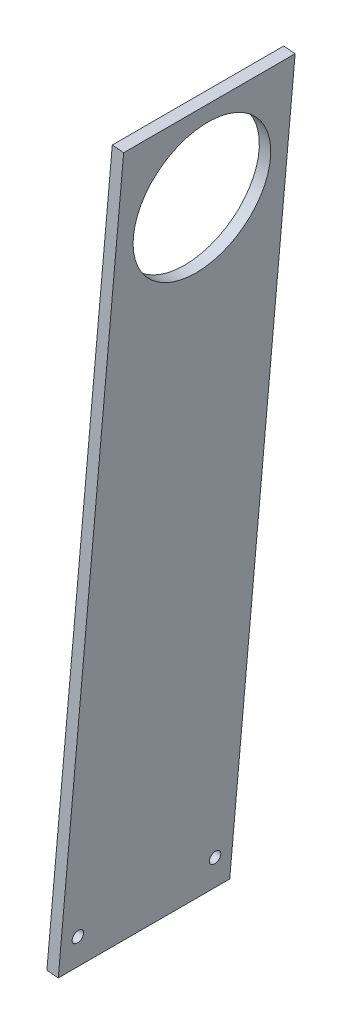
SolidWorks part; units mm, degrees
ref_plane "Front Plane" through (0, 0, 0) normal (0, 0, 1) x (1, 0, 0)
ref_plane "Top Plane" through (0, 0, 0) normal (0, 1, 0) x (1, 0, 0)
ref_plane "Right Plane" through (0, 0, 0) normal (1, 0, 0) x (0, 0, -1)
sketch "Sketch1" plane through (0, 0, 0) normal (0, 0, 1) x (1, 0, 0)
  line L0 (0, 0) -> (36.6665, 419.1) construction
  line L1 (36.6665, 419.1) -> (155.7226, 419.1) construction
  line L2 (155.7226, 419.1) -> (155.7226, 0) construction
  line L3 (155.7226, 0) -> (0, 0) construction
  line L4 (155.7226, -1000) -> (155.7226, 49000) construction
  line L5 (1.8042, 20.6221) -> (36.6665, 419.1) construction
  line L6 (1.8042, 20.6221) -> (41.652, 17.1359) construction
  line L7 (36.6665, 419.1) -> (76.5143, 415.6138) construction
  line L8 (41.652, 17.1359) -> (76.5143, 415.6138) construction
  line L9 (60.4726, -1000) -> (60.4726, 49000) construction
  line L10 (-52.7184, 317.5) -> (-128.6284, 324.1413) construction
  line L11 (-30.1965, 414.3375) -> (36.6601, 414.3375) construction
  line L12 (-1162.1335, 304.8) -> (48837.8665, 304.8) construction
  line L13 (-130.0274, 292.1) -> (-53.8274, 292.1) construction
  line L14 (-128.6284, 324.1413) -> (-53.8274, 292.1) construction
  line L15 (-52.7184, 317.5) -> (-130.0274, 292.1) construction
  line L16 (36.6601, 338.1375) -> (-30.1965, 338.1375) construction
  line L17 (-138.1172, 324.9714) -> (27.1662, 310.511)
  line L18 (-138.1172, 324.9714) -> (-137.5638, 331.2973)
  line L19 (-137.5638, 331.2973) -> (36.6665, 419.1)
  line L20 (36.6665, 419.1) -> (104.9226, 419.1)
  line L21 (104.9226, 419.1) -> (104.9226, 0) construction
  line L22 (27.1662, 310.511) -> (0.3389, 3.8741)
  line L23 (0.3389, 3.8741) -> (44.6198, 0)
  line L24 (44.6198, 0) -> (104.9226, 0)
  line L25 (104.9226, 419.1) -> (155.7226, 311.15)
  line L26 (155.7226, 311.15) -> (155.7226, 304.8)
  line L27 (155.7226, 304.8) -> (104.9226, 280.8941)
  line L28 (104.9226, 280.8941) -> (104.9226, 0)
  arc A0 (-128.6284, 324.1413) -> (-30.1965, 414.3375) centre (-30.1965, 315.5296) cw construction
  arc A1 (69.9976, 304.8) -> (36.6601, 338.1375) centre (36.6601, 304.8) ccw construction
  arc A2 (146.1976, 304.8) -> (36.6601, 414.3375) centre (36.6601, 304.8) ccw construction
  arc A3 (-52.7184, 317.5) -> (-30.1965, 338.1375) centre (-30.1965, 315.5296) cw construction
  point P7 (54.1226, 400.05)
  point P17 (146.1976, 304.8)
  point P18 (69.9976, 304.8)
  dimension "D9" = 9.525
  dimension "D14" = 25.4
  dimension "D1" = 419.1
  dimension "D2" = 101.6
  dimension "D3" = 19.05
  dimension "D4" = 19.05
  dimension "D5" = 85
  dimension "D6" = 40
  dimension "D7" = 400
  dimension "D8" = 95.25
  dimension "D10" = 9.525
  dimension "D11" = 114.3
  dimension "D12" = 76.2
  dimension "D13" = 9.525
  dimension "D15" = 127
  dimension "D16" = 9.525
  dimension "D17" = 209.55
  dimension "D18" = 6.35
  dimension "D19" = 50.8
  dimension "D20" = 44.45
  dimension "D21" = 6.35
sketch "Sketch2" plane through (0, 0, 0) normal (0, 0, 1) x (1, 0, 0)
  line L0 (6.6648, 3.3206) -> (0.3389, 3.8741)
  line L1 (6.6648, 3.3206) -> (42.9923, 418.5466)
  line L2 (0.3389, 3.8741) -> (36.6665, 419.1)
  line L3 (42.9923, 418.5466) -> (36.6665, 419.1)
  line L4 (0.3389, 3.8741) -> (44.6198, 0) construction
  line L5 (36.6665, 419.1) -> (104.9226, 419.1) construction
  dimension "D2" = 6.35
extrude "Boss-Extrude1" add sketch "Sketch2" along normal blind 95.25
sketch "Sketch3" plane through (0, 0, 0) normal (-0.9962, 0.0872, 0) x (0, 0, 1)
  line L0 (47.625, 373.0759) -> (47.625, 420.7009) construction
  line L1 (95.25, 420.7009) -> (0, 420.7009) construction
  circle A0 centre (47.625, 373.0759) radius 38.1
  dimension "D1" = 76.2
  dimension "D2" = 47.625
extrude "Cut-Extrude1" cut sketch "Sketch3" against normal through all
sketch "Sketch4" plane through (0, 0, 0) normal (-0.9962, 0.0872, 0) x (0, 0, 1)
  line L0 (95.25, 3.8889) -> (0, 3.8889) construction
  line L1 (9.525, -11.9861) -> (85.725, -11.9861) construction
  line L2 (9.525, -11.9861) -> (9.525, 19.7639) construction
  line L3 (9.525, 19.7639) -> (85.725, 19.7639) construction
  line L4 (85.725, -11.9861) -> (85.725, 19.7639) construction
  line L5 (9.525, -11.9861) -> (85.725, 19.7639) construction
  line L6 (9.525, 19.7639) -> (85.725, -11.9861) construction
  line L7 (0, 420.7009) -> (0, 3.8889) construction
  circle A0 centre (9.525, 19.7639) radius 3.175
  circle A1 centre (85.725, 19.7639) radius 3.175
  point P0 (47.625, 3.8889)
  dimension "D3" = 6.35
  dimension "D1" = 9.525
  dimension "D2" = 15.875
extrude "Cut-Extrude2" cut sketch "Sketch4" against normal through all
